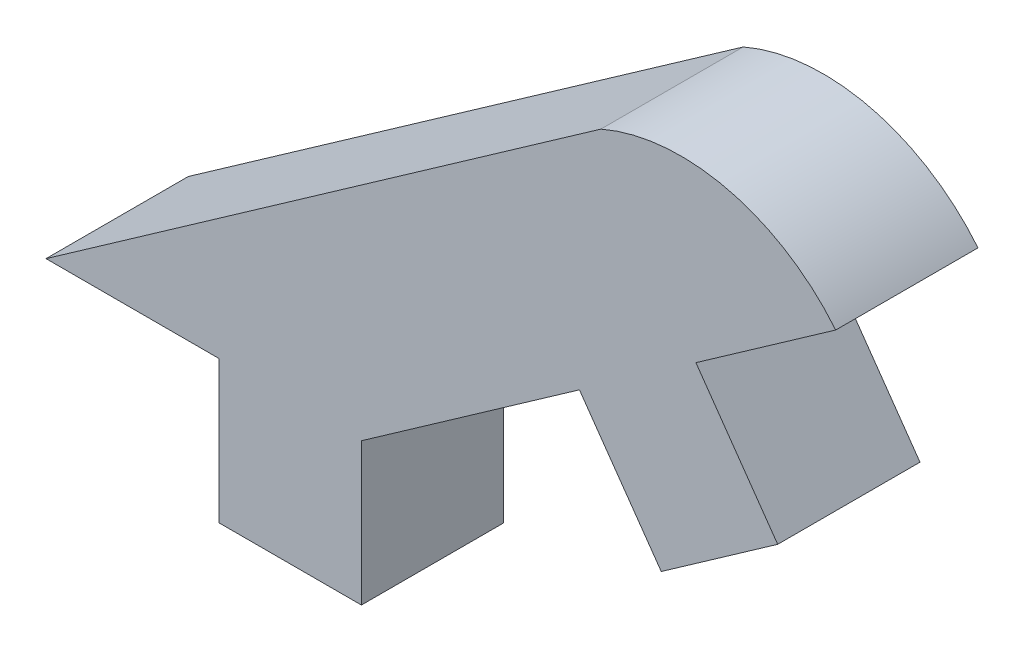
SolidWorks part; units mm, degrees
ref_plane "Front Plane" through (0, 0, 0) normal (0, 0, 1) x (1, 0, 0)
ref_plane "Top Plane" through (0, 0, 0) normal (0, 1, 0) x (1, 0, 0)
ref_plane "Right Plane" through (0, 0, 0) normal (1, 0, 0) x (0, 0, -1)
sketch "Sketch1" plane through (0, 0, 0) normal (0, 0, 1) x (1, 0, 0)
  line L0 (26.7036, 0) -> (26.7036, -1.524)
  line L1 (26.7036, -1.524) -> (28.2276, -1.524)
  line L2 (28.2276, -1.524) -> (28.2276, 0)
  line L3 (28.2276, 0) -> (30.5628, 1.6397)
  line L4 (26.7036, 0) -> (24.8497, 0)
  line L5 (24.8497, 0) -> (30.7924, 4.1728)
  line L6 (30.5628, 1.6397) -> (31.4385, 0.3924)
  line L7 (31.4385, 0.3924) -> (32.6858, 1.2682)
  line L8 (32.6858, 1.2682) -> (31.81, 2.5154)
  line L9 (31.81, 2.5154) -> (33.307, 3.5665)
  arc A0 (33.307, 3.5665) -> (30.7924, 4.1728) centre (31.6508, 2.215) ccw
extrude "Boss-Extrude1" add sketch "Sketch1" along normal blind 1.524
